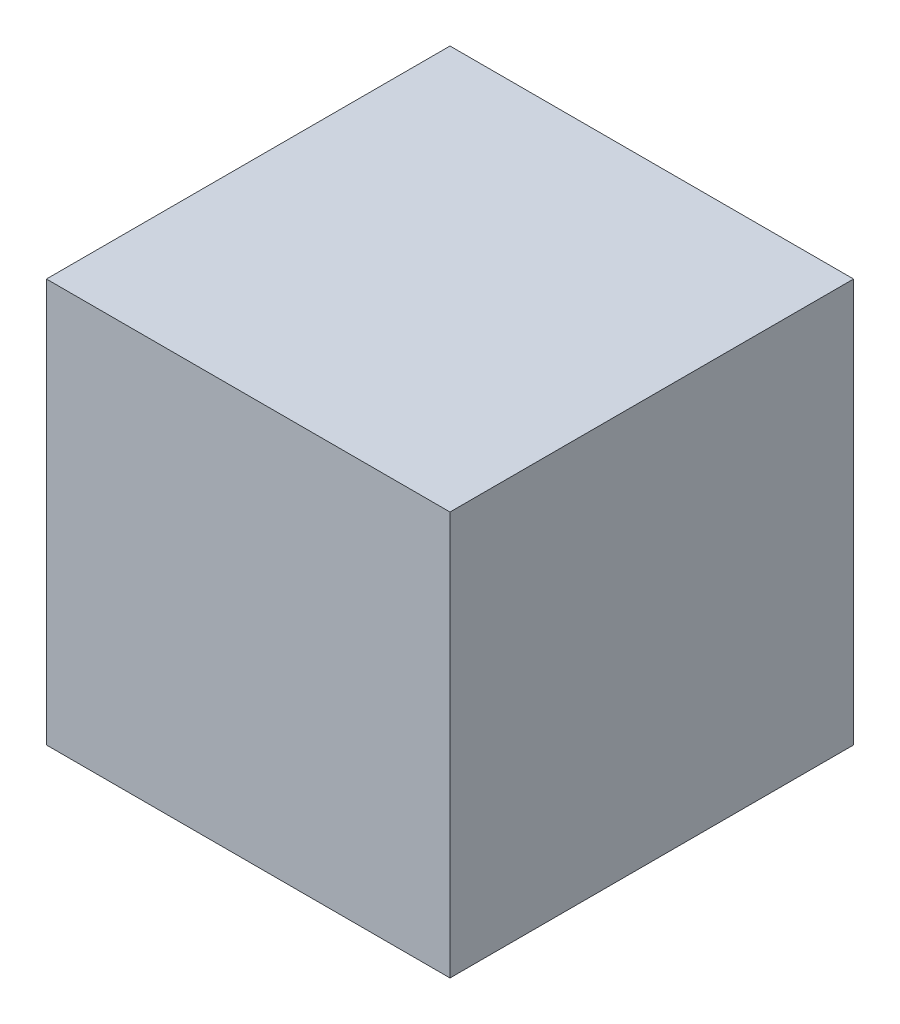
SolidWorks part; units mm, degrees
ref_plane "前视基准面" through (0, 0, 0) normal (0, 0, 1) x (1, 0, 0)
ref_plane "上视基准面" through (0, 0, 0) normal (0, 1, 0) x (1, 0, 0)
ref_plane "右视基准面" through (0, 0, 0) normal (1, 0, 0) x (0, 0, -1)
sketch "草图1" plane through (0, 0, 0) normal (0, 0, 1) x (1, 0, 0)
  line L1 (0, 0) -> (10, 0)
  line L2 (0, 0) -> (0, 10)
  line L3 (0, 10) -> (10, 10)
  line L4 (10, 0) -> (10, 10)
  dimension "D1" = 10
  dimension "D2" = 10
extrude "凸台-拉伸1" add sketch "草图1" along normal blind 10
